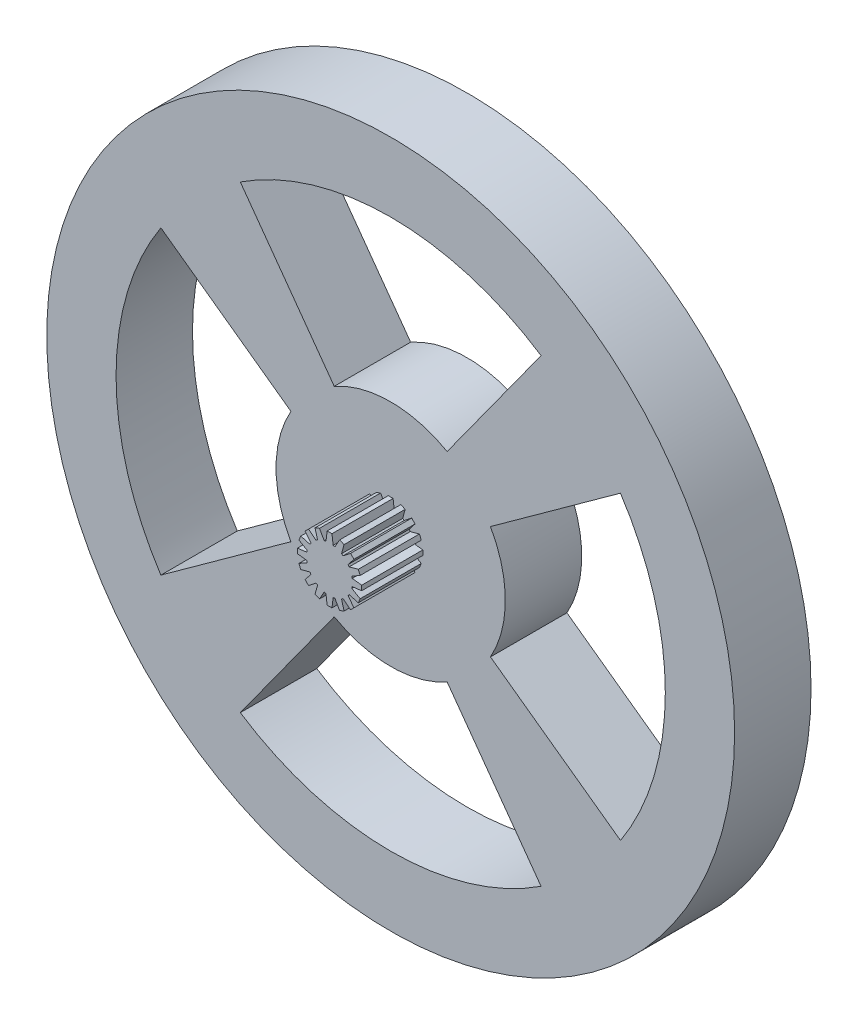
SolidWorks part; units mm, degrees
ref_plane "Plano frontal" through (0, 0, 0) normal (0, 0, 1) x (1, 0, 0)
ref_plane "Plano superior" through (0, 0, 0) normal (0, 1, 0) x (1, 0, 0)
ref_plane "Plano direito" through (0, 0, 0) normal (1, 0, 0) x (0, 0, -1)
sketch "Esboço1" plane through (0, 0, 0) normal (0, 0, 1) x (1, 0, 0)
  circle A0 centre (0, 0) radius 45
extrude "Ressalto-extrusão1" add sketch "Esboço1" along normal blind 10
sketch "Esboço2" plane through (0, 0, 10) normal (0, 0, 1) x (1, 0, 0)
  line L0 (-7.3864, 13.0553) -> (-19.6758, 30.0668)
  line L1 (7.3864, 13.0553) -> (19.6758, 30.0668)
  line L2 (0, 0) -> (0, 49.6392) construction
  arc A0 (7.477, 13.0037) -> (-7.3864, 13.0553) centre (0, 0) ccw
  arc A1 (-19.6758, 30.0668) -> (19.6758, 30.0668) centre (0, 0) cw
  arc A2 (-7.477, 13.0037) -> (7.3864, 13.0553) centre (0, 0) cw
extrude "Corte-extrusão1" cut sketch "Esboço2" against normal blind 10 contours L2 A0 L1 A1 | A2 L2 A1 L0
pattern_circular "PadrãoCircular1" count 4 over 360 about axis through (0, 0, 0) along (0, 0, 1) of "Corte-extrusão1"
sketch "Esboço3" plane through (0, 0, 10) normal (0, 0, 1) x (1, 0, 0)
  circle A0 centre (0, 0) radius 3
extrude "Ressalto-extrusão2" add sketch "Esboço3" along normal blind 8
sketch "Esboço4" plane through (0, 0, 18) normal (0, 0, 1) x (1, 0, 0)
  line L0 (0, 0) -> (0, 7.8808) construction
  line L1 (-0.5, 2.6951) -> (0.5, 2.6951)
  line L2 (0, 2.6951) -> (0, 4.2033)
  line L3 (0.3148, 4.2033) -> (-0.3148, 4.2033)
  line L4 (-0.3148, 4.2033) -> (-0.5, 2.6951)
  line L5 (0.3148, 4.2033) -> (0.5, 2.6951)
extrude "Ressalto-extrusão3" add sketch "Esboço4" against normal blind 8 contours L5 L1 L4 L3
pattern_circular "PadrãoCircular2" count 16 over 360 about axis through (0, 0, 0) along (0, 0, 1) of "Ressalto-extrusão3"
